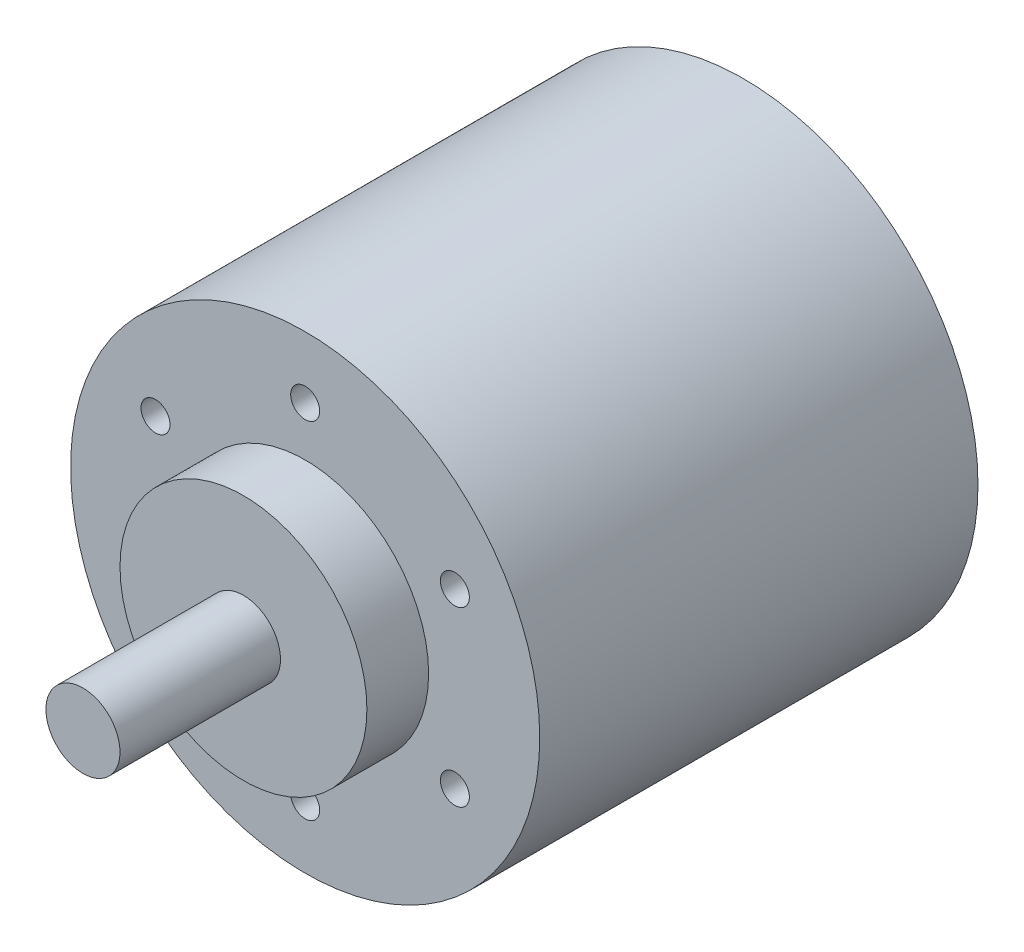
SolidWorks part; units mm, degrees
ref_plane "Front Plane" through (0, 0, 0) normal (0, 0, 1) x (1, 0, 0)
ref_plane "Top Plane" through (0, 0, 0) normal (0, 1, 0) x (1, 0, 0)
ref_plane "Right Plane" through (0, 0, 0) normal (1, 0, 0) x (0, 0, -1)
sketch "Sketch1" plane through (0, 0, 0) normal (0, 0, 1) x (1, 0, 0)
  circle A0 centre (0, 0) radius 19
  dimension "D1" = 38
extrude "Boss-Extrude1" add sketch "Sketch1" against normal blind 35.5
sketch "Sketch2" plane through (0, 0, 0) normal (0, 0, 1) x (1, 0, 0)
  circle A0 centre (0, 0) radius 10
  dimension "D1" = 20
extrude "Boss-Extrude2" add sketch "Sketch2" along normal blind 5
sketch "Sketch3" plane through (0, 0, 5) normal (0, 0, 1) x (1, 0, 0)
  circle A0 centre (0, 0) radius 3
  dimension "D1" = 6
extrude "Boss-Extrude3" add sketch "Sketch3" along normal blind 13
sketch "Sketch4" plane through (0, 0, 0) normal (0, 0, 1) x (1, 0, 0)
  line L0 (0, 0) -> (0, 19) construction
  circle A0 centre (0, 14) radius 1.1743
  circle A1 centre (0, 0) radius 19 construction
  dimension "D1" = 14
extrude "Cut-Extrude1" cut sketch "Sketch4" against normal blind 5
pattern_circular "CirPattern1" count 6 every 60 about axis through (0, 0, 0) along (0, 0, 1) of "Cut-Extrude1"
